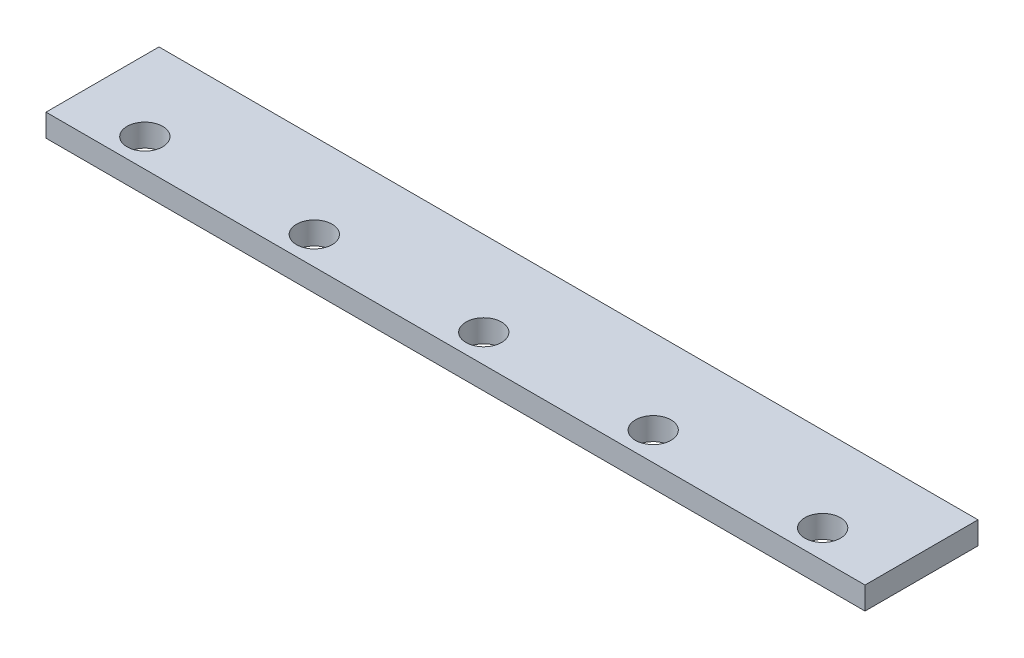
SolidWorks part; units mm, degrees
ref_plane "Front Plane" through (0, 0, 0) normal (0, 0, 1) x (1, 0, 0)
ref_plane "Top Plane" through (0, 0, 0) normal (0, 1, 0) x (1, 0, 0)
ref_plane "Right Plane" through (0, 0, 0) normal (1, 0, 0) x (0, 0, -1)
sketch "Sketch1" plane through (0, 0, 0) normal (0, 1, 0) x (1, 0, 0)
  line L1 (0, 0) -> (580, 0)
  line L2 (0, 0) -> (0, -80)
  line L3 (0, -80) -> (580, -80)
  line L4 (580, 0) -> (580, -80)
  dimension "D1" = 80
  dimension "D2" = 580
extrude "Boss-Extrude1" add sketch "Sketch1" along normal blind 16
sketch "Sketch2" plane through (0, 0, 0) normal (0, 1, 0) x (1, 0, 0)
  circle A0 centre (50, -60) radius 12.6
  dimension "D1" = 25.2
extrude "Cut-Extrude4" cut sketch "Sketch2" along normal blind 18
pattern_linear "LPattern1" count 5 spacing 120 along (1, 0, 0) of "Cut-Extrude4"
